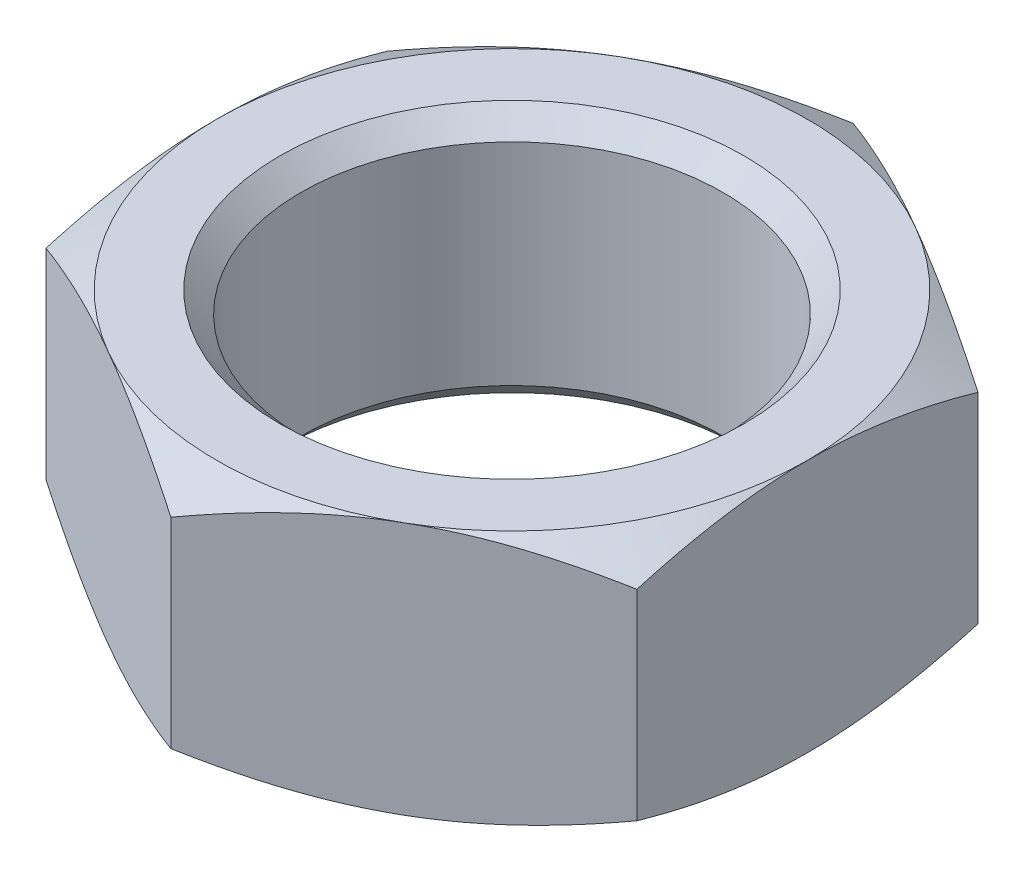
SolidWorks part; units mm, degrees
ref_plane "Front Plane" through (0, 0, 0) normal (0, 0, 1) x (1, 0, 0)
ref_plane "Top Plane" through (0, 0, 0) normal (0, 1, 0) x (1, 0, 0)
ref_plane "Right Plane" through (0, 0, 0) normal (1, 0, 0) x (0, 0, -1)
sketch "Sketch1" plane through (0, 0, 0) normal (0, 1, 0) x (1, 0, 0)
  line L1 (0, -16.1658) -> (14, -8.0829)
  line L2 (14, -8.0829) -> (14, 8.0829)
  line L3 (14, 8.0829) -> (0, 16.1658)
  line L4 (0, 16.1658) -> (-14, 8.0829)
  line L5 (-14, 8.0829) -> (-14, -8.0829)
  line L6 (-14, -8.0829) -> (0, -16.1658)
  circle A0 centre (0, 0) radius 14 construction
  dimension "D1" = 28
extrude "Boss-Extrude1" add sketch "Sketch1" along normal mid plane 12
sketch "Sketch2" plane through (0, 6, 0) normal (0, 1, 0) x (1, 0, 0)
  line L0 (14, 8.0829) -> (0, 16.1658) construction
  circle A0 centre (0, 0) radius 14
extrude "Cut-Extrude1" cut sketch "Sketch2" against normal blind 12 draft 60 flip side to cut
mirror "Mirror1" about plane through (0, 0, 0) normal (0, 1, 0) of "Cut-Extrude1"
sketch "Sketch3" plane through (0, 6, 0) normal (0, 1, 0) x (1, 0, 0)
  circle A0 centre (0, 0) radius 10
  dimension "D1" = 20
extrude "Cut-Extrude2" cut sketch "Sketch3" against normal through all
chamfer "Chamfer1" distance 1 angle 45 2 edges at (0, -6, 10) (0, 6, 10)
